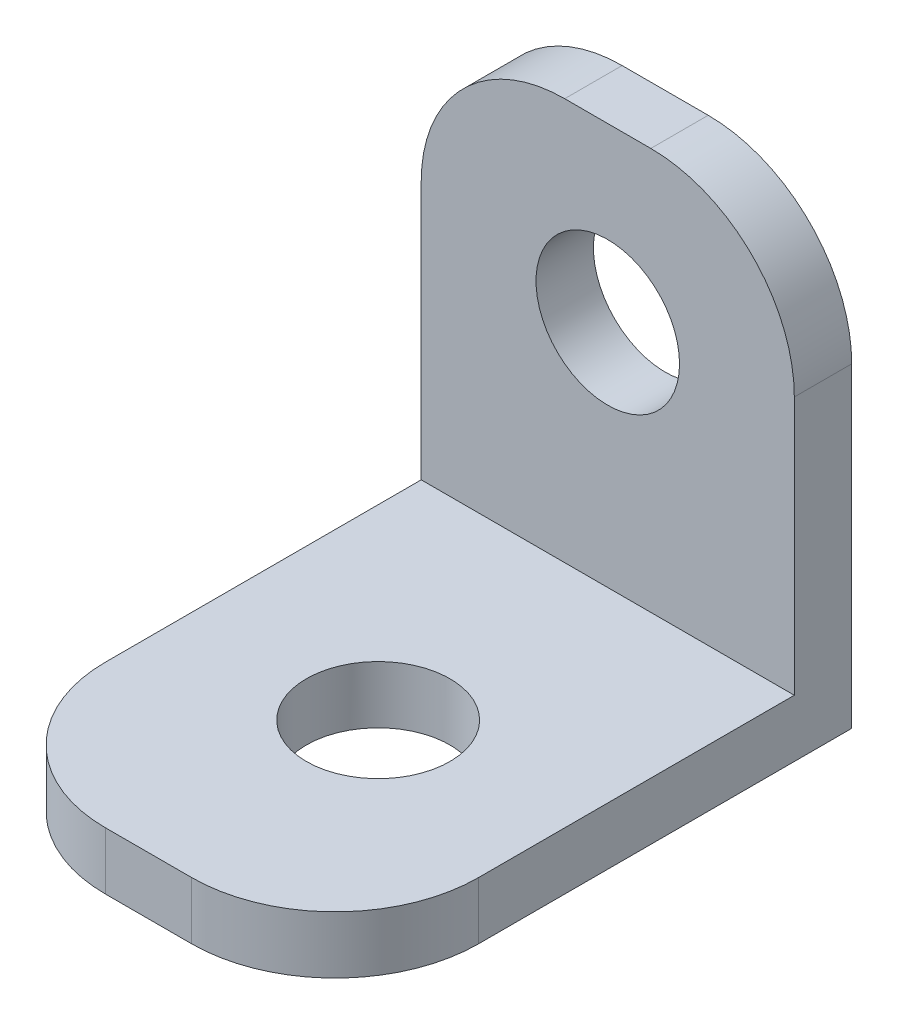
SolidWorks part; units mm, degrees
ref_plane "Front Plane" through (0, 0, 0) normal (0, 0, 1) x (1, 0, 0)
ref_plane "Top Plane" through (0, 0, 0) normal (0, 1, 0) x (1, 0, 0)
ref_plane "Right Plane" through (0, 0, 0) normal (1, 0, 0) x (0, 0, -1)
sketch "Sketch1" plane through (0, 0, 0) normal (0, 0, 1) x (1, 0, 0)
  line L1 (6.5, -8) -> (-6.5, -8)
  line L2 (6.5, -8) -> (6.5, 8)
  line L3 (6.5, 8) -> (-6.5, 8)
  line L4 (-6.5, -8) -> (-6.5, 8)
  line L5 (6.5, -8) -> (-6.5, 8) construction
  line L6 (6.5, 8) -> (-6.5, -8) construction
  circle A0 centre (0, 2) radius 2.5
  point P0 (0, 0)
  dimension "D4" = 5
  dimension "D1" = 16
  dimension "D2" = 13
  dimension "D3" = 10
extrude "Boss-Extrude1" add sketch "Sketch1" along normal blind 2
fillet "Fillet1" radius 5 2 edges at (-6.5, 8, 1) (6.5, 8, 1)
sketch "Sketch2" plane through (0, 0, 2) normal (0, 0, 1) x (1, 0, 0)
  line L0 (-6.5, -8) -> (6.5, -8) construction
  line L1 (-6.5, -8) -> (6.5, -8)
  line L2 (-6.5, -8) -> (-6.5, -6)
  line L3 (-6.5, 3) -> (-6.5, -8) construction
  line L4 (-6.5, -6) -> (6.5, -6)
  line L5 (6.5, -8) -> (6.5, 3) construction
  line L6 (6.5, -6) -> (6.5, -8)
  dimension "D1" = 2
extrude "Boss-Extrude2" add sketch "Sketch2" along normal blind 16
fillet "Fillet2" radius 5 2 edges at (6.5, -7, 18) (-6.5, -7, 18)
sketch "Sketch3" plane through (0, -6, 0) normal (0, 1, 0) x (1, 0, 0)
  line L0 (6.5, 0) -> (1.5, 0) construction
  circle A0 centre (0, -10) radius 2.5
  dimension "D2" = 5
  dimension "D1" = 10
extrude "Cut-Extrude1" cut sketch "Sketch3" against normal blind 16
